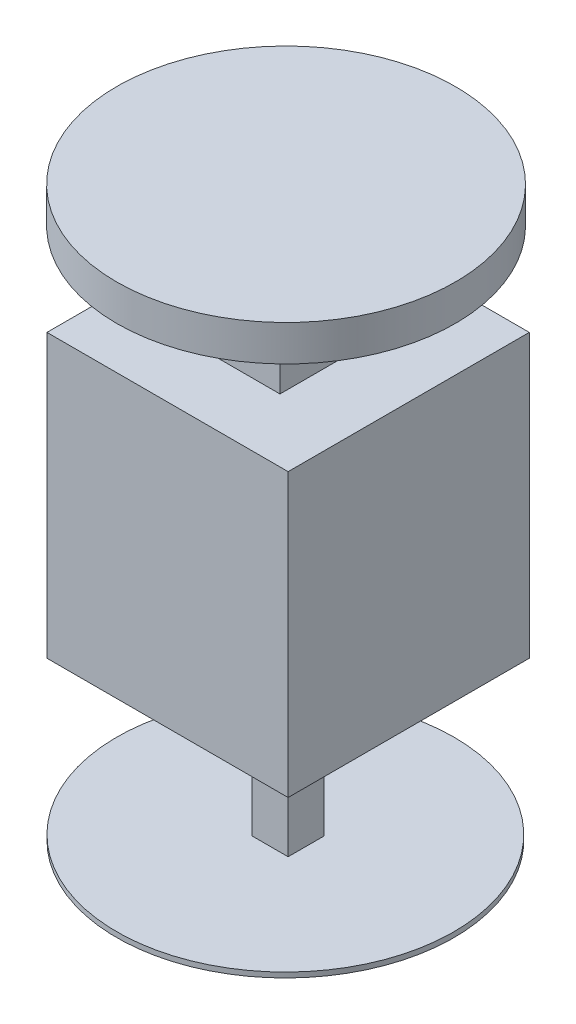
SolidWorks part; units mm, degrees
ref_plane "Front Plane" through (0, 0, 0) normal (0, 0, 1) x (1, 0, 0)
ref_plane "Top Plane" through (0, 0, 0) normal (0, 1, 0) x (1, 0, 0)
ref_plane "Right Plane" through (0, 0, 0) normal (1, 0, 0) x (0, 0, -1)
sketch "Sketch1" plane through (0, 0, 0) normal (0, 1, 0) x (1, 0, 0)
  line L1 (0, 0) -> (47, 0)
  line L2 (0, 0) -> (0, 47)
  line L3 (0, 47) -> (47, 47)
  line L4 (47, 0) -> (47, 47)
  dimension "D1" = 47
  dimension "D2" = 47
extrude "Boss-Extrude1" add sketch "Sketch1" along normal blind 85
sketch "Sketch2" plane through (0, 0, 0) normal (0, 0, 1) x (1, 0, 0)
  line L0 (0, 85) -> (0, 0) construction
  line L1 (47, 0) -> (0, 0)
  line L2 (47, 0) -> (47, 30)
  line L3 (47, 30) -> (0, 30)
  line L4 (0, 0) -> (0, 30)
  dimension "D1" = 30
extrude "Cut-Extrude1" cut sketch "Sketch2" against normal blind 20
sketch "Sketch3" plane through (0, 0, 0) normal (-1, 0, 0) x (0, 0, 1)
  line L0 (-47, 85) -> (-47, 0) construction
  line L1 (-20, 0) -> (-47, 0)
  line L2 (-20, 0) -> (-20, 29.9492)
  line L3 (-20, 29.9492) -> (-47, 29.9492)
  line L4 (-47, 0) -> (-47, 29.9492)
extrude "Cut-Extrude2" cut sketch "Sketch3" against normal blind 20
sketch "Sketch4" plane through (0, 0, -47) normal (0, 0, -1) x (-1, 0, 0)
  line L1 (-20, 0) -> (-47, 0)
  line L2 (-20, 0) -> (-20, 30)
  line L3 (-20, 30) -> (-47, 30)
  line L4 (-47, 0) -> (-47, 30)
extrude "Cut-Extrude3" cut sketch "Sketch4" against normal blind 20
sketch "Sketch5" plane through (47, 0, 0) normal (1, 0, 0) x (0, 0, -1)
  line L1 (20, 0) -> (27, 0)
  line L2 (20, 0) -> (20, 30)
  line L3 (20, 30) -> (27, 30)
  line L4 (27, 0) -> (27, 30)
extrude "Cut-Extrude4" cut sketch "Sketch5" against normal blind 20
sketch "Sketch6" plane through (0, 85, 0) normal (0, 1, 0) x (1, 0, 0)
  line L1 (15.2221, 31.2339) -> (33.1023, 31.2339)
  line L2 (15.2221, 31.2339) -> (15.2221, 12.313)
  line L3 (15.2221, 12.313) -> (33.1023, 12.313)
  line L4 (33.1023, 31.2339) -> (33.1023, 12.313)
extrude "Boss-Extrude2" add sketch "Sketch6" along normal blind 18
sketch "Sketch7" plane through (0, 103, 0) normal (0, 1, 0) x (1, 0, 0)
  circle A0 centre (23.299, 23.299) radius 33
  dimension "D1" = 66
extrude "Boss-Extrude4" add sketch "Sketch7" along normal blind 7
sketch "Sketch9" plane through (0, 0, 0) normal (0, -1, 0) x (1, 0, 0)
  circle A0 centre (22.9615, -23.5) radius 32.8555
extrude "Boss-Extrude5" add sketch "Sketch9" along normal blind 1
